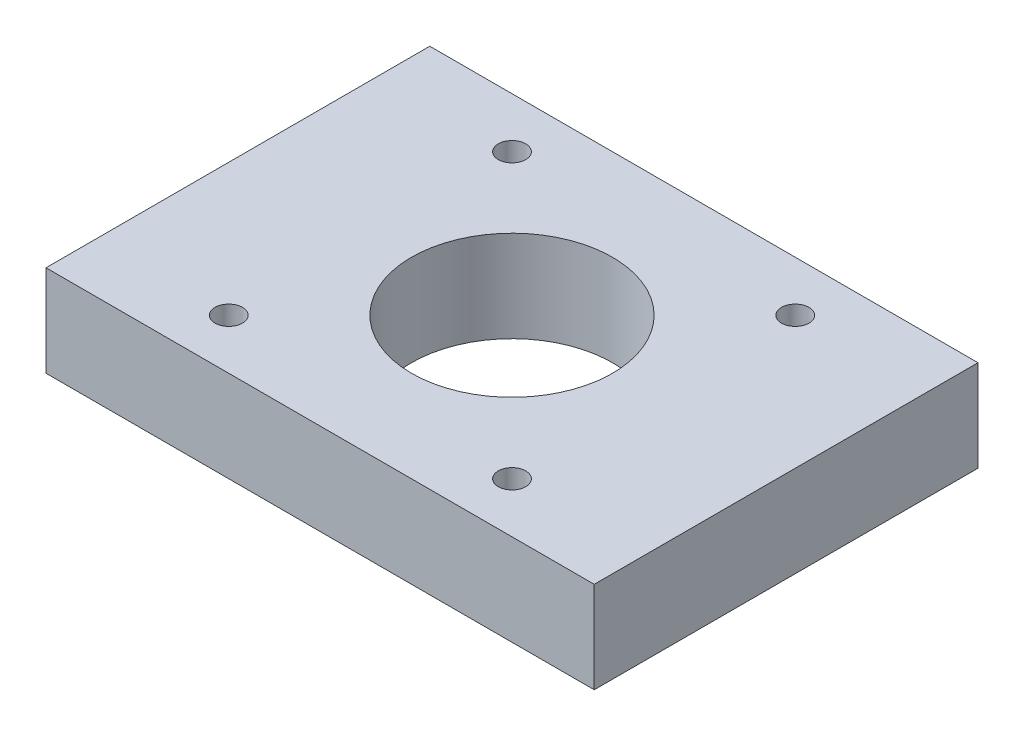
SolidWorks part; units mm, degrees
ref_plane "Front Plane" through (0, 0, 0) normal (0, 0, 1) x (1, 0, 0)
ref_plane "Top Plane" through (0, 0, 0) normal (0, 1, 0) x (1, 0, 0)
ref_plane "Right Plane" through (0, 0, 0) normal (1, 0, 0) x (0, 0, -1)
sketch "Sketch1" plane through (0, 0, 0) normal (0, 0, 1) x (1, 0, 0)
  line L1 (-30, 62.7715) -> (30, 62.7715)
  line L2 (-30, 62.7715) -> (-30, 52.7715)
  line L3 (-30, 52.7715) -> (30, 52.7715)
  line L4 (30, 62.7715) -> (30, 52.7715)
  dimension "D1" = 60
  dimension "D2" = 10
extrude "Boss-Extrude1" add sketch "Sketch1" along normal blind 42
sketch "Sketch2" plane through (0, 62.7715, 0) normal (0, 1, 0) x (1, 0, 0)
  circle A1 centre (0, -21) radius 11
  circle A2 centre (0, -21) radius 11
  circle A3 centre (-15.5, -36.5) radius 1.5
  circle A4 centre (-15.5, -36.5) radius 1.5
  circle A5 centre (15.5, -36.5) radius 1.5
  circle A6 centre (15.5, -36.5) radius 1.5
  circle A7 centre (-15.5, -5.5) radius 1.5
  circle A8 centre (-15.5, -5.5) radius 1.5
  circle A9 centre (15.5, -5.5) radius 1.5
  circle A10 centre (15.5, -5.5) radius 1.5
  dimension "D1" = 0
  dimension "D2" = 0
  dimension "D3" = 0
  dimension "D4" = 0
  dimension "D5" = 0
extrude "Cut-Extrude1" cut sketch "Sketch2" against normal through all
sketch "Sketch3" plane through (0, 52.7715, 0) normal (0, -1, 0) x (1, 0, 0)
  circle A0 centre (-15.5, 36.5) radius 2.85
  circle A1 centre (15.5, 36.5) radius 2.85
  circle A2 centre (15.5, 5.5) radius 2.85
  circle A3 centre (-15.5, 5.5) radius 2.85
  dimension "D1" = 5.7
extrude "Cut-Extrude2" cut sketch "Sketch3" against normal blind 3
